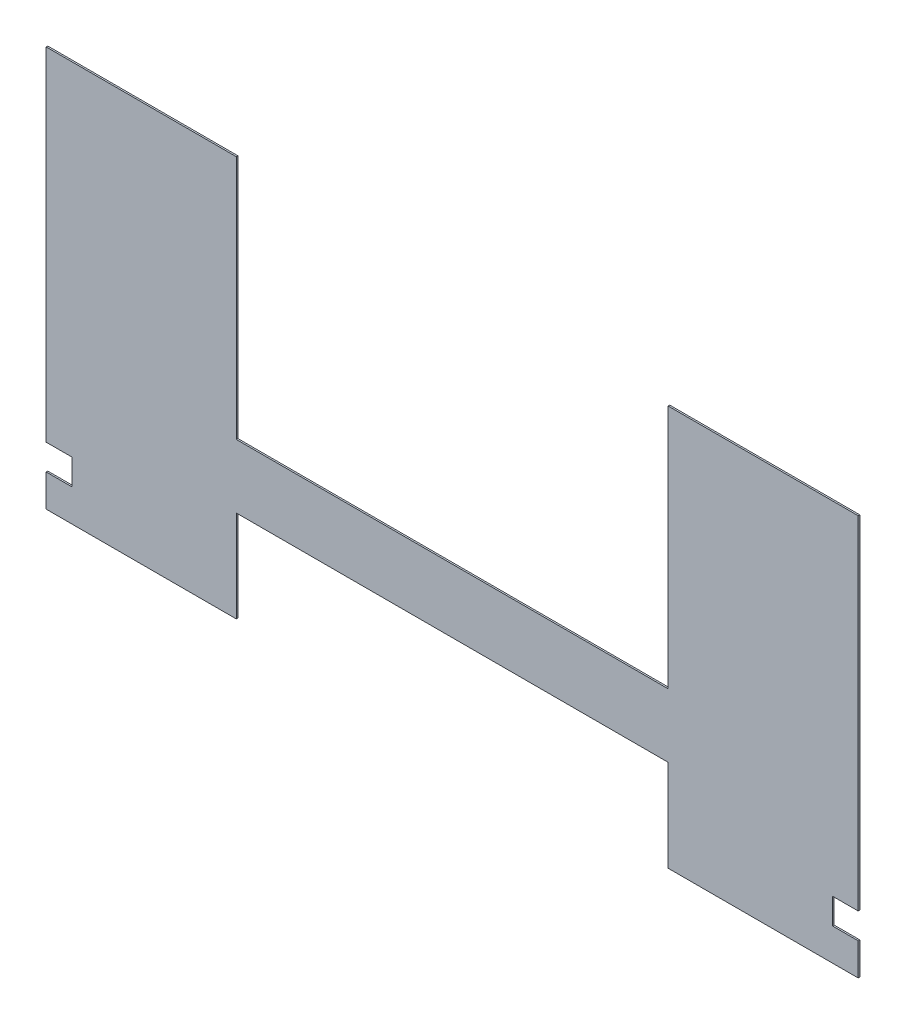
SolidWorks part; units mm, degrees
material "6061-T6 (SS)"
ref_plane "Front Plane" through (0, 0, 0) normal (0, 0, 1) x (1, 0, 0)
ref_plane "Top Plane" through (0, 0, 0) normal (0, 1, 0) x (1, 0, 0)
ref_plane "Right Plane" through (0, 0, 0) normal (1, 0, 0) x (0, 0, -1)
sketch "Sketch1" plane through (0, 0, 0) normal (0, 0, 1) x (1, 0, 0)
  line L0 (-400.05, 241.3) -> (-400.05, -153.162)
  line L1 (-400.05, -153.162) -> (-212.725, -153.162)
  line L2 (-212.725, -153.162) -> (-212.725, -62.738)
  line L3 (-212.725, -62.738) -> (212.725, -62.738)
  line L4 (212.725, -62.738) -> (212.725, -153.162)
  line L5 (212.725, -153.162) -> (400.05, -153.162)
  line L6 (400.05, -153.162) -> (400.05, 241.3)
  line L7 (400.05, 241.3) -> (212.725, 241.3)
  line L8 (212.725, 241.3) -> (212.725, 0)
  line L9 (212.725, 0) -> (-212.725, 0)
  line L10 (-212.725, 0) -> (-212.725, 241.3)
  line L11 (-212.725, 241.3) -> (-400.05, 241.3)
  dimension "D1" = 90.424
  dimension "D2" = 394.462
  dimension "D3" = 187.325
  dimension "D4" = 153.162
  dimension "D5" = 425.45
extrude "Boss-Extrude1" add sketch "Sketch1" along normal blind 1.5875
sketch "Sketch2" plane through (0, 0, 0) normal (0, 0, -1) x (-1, 0, 0)
  line L0 (-212.725, -134.112) -> (-400.05, -134.112) construction
  line L1 (-374.65, -121.412) -> (-400.05, -121.412)
  line L2 (-374.65, -121.412) -> (-374.65, -96.012)
  line L3 (-374.65, -96.012) -> (-400.05, -96.012)
  line L4 (-400.05, -121.412) -> (-400.05, -96.012)
  line L5 (-374.65, -121.412) -> (-400.05, -96.012) construction
  line L6 (-374.65, -96.012) -> (-400.05, -121.412) construction
  line L7 (-400.05, -153.162) -> (-400.05, 241.3) construction
  point P0 (-387.35, -108.712)
  dimension "D1" = 25.4
  dimension "D2" = 25.4
  dimension "D3" = 12.7
  dimension "D4" = 0
extrude "Cut-Extrude1" cut sketch "Sketch2" against normal through all
sketch "Sketch3" plane through (0, 0, 0) normal (0, 0, -1) x (-1, 0, 0)
  line L0 (400.05, -134.112) -> (212.725, -134.112) construction
  line L1 (400.05, -121.412) -> (374.65, -121.412)
  line L2 (400.05, -121.412) -> (400.05, -96.012)
  line L3 (400.05, -96.012) -> (374.65, -96.012)
  line L4 (374.65, -121.412) -> (374.65, -96.012)
  line L5 (400.05, -121.412) -> (374.65, -96.012) construction
  line L6 (400.05, -96.012) -> (374.65, -121.412) construction
  line L7 (400.05, 241.3) -> (400.05, -153.162) construction
  point P0 (387.35, -108.712)
  dimension "D1" = 25.4
  dimension "D2" = 25.4
  dimension "D3" = 12.7
  dimension "D4" = 0
extrude "Cut-Extrude2" cut sketch "Sketch3" against normal through all
